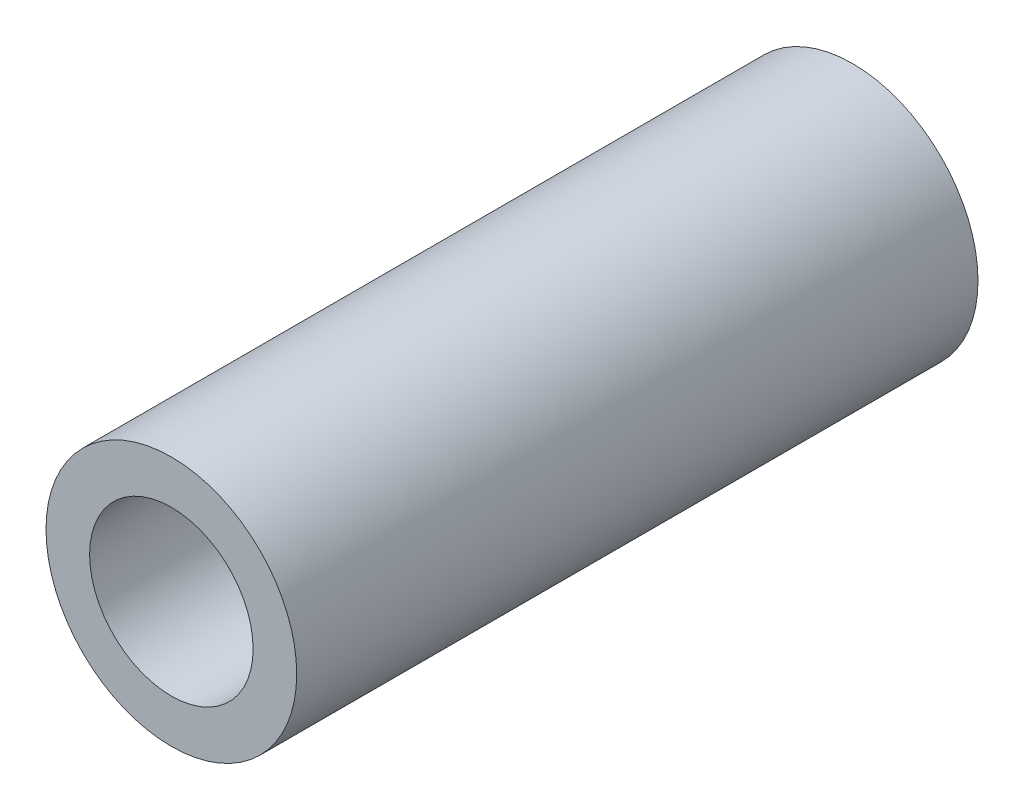
SolidWorks part; units mm, degrees
ref_plane "Front Plane" through (0, 0, 0) normal (0, 0, 1) x (1, 0, 0)
ref_plane "Top Plane" through (0, 0, 0) normal (0, 1, 0) x (1, 0, 0)
ref_plane "Right Plane" through (0, 0, 0) normal (1, 0, 0) x (0, 0, -1)
sketch "Sketch1" plane through (0, 0, 0) normal (0, 0, 1) x (1, 0, 0)
  circle A0 centre (0, 0) radius 4.6
  circle A1 centre (0, 0) radius 3
  dimension "D1" = 9.2
  dimension "D2" = 6
extrude "Boss-Extrude1" add sketch "Sketch1" against normal blind 25
